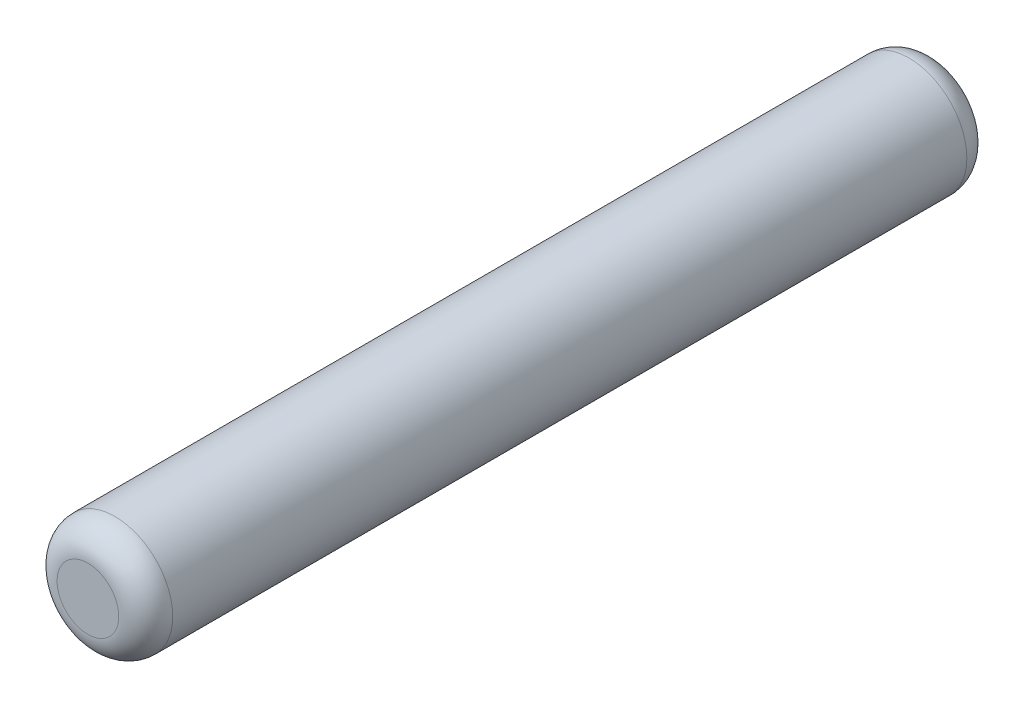
SolidWorks part; units mm, degrees
ref_plane "Front" through (0, 0, 0) normal (0, 0, 1) x (1, 0, 0)
ref_plane "Top" through (0, 0, 0) normal (0, 1, 0) x (1, 0, 0)
ref_plane "Right" through (0, 0, 0) normal (1, 0, 0) x (0, 0, -1)
sketch "Sketch1" plane through (0, 0, 0) normal (0, 0, 1) x (1, 0, 0)
  circle A0 centre (0, 0) radius 0.75
  dimension "D1" = 1.5
extrude "Boss-Extrude1" add sketch "Sketch1" along normal mid plane 11
fillet "Fillet1" radius 0.35 2 edges at (0.75, 0, -5.5) (0.75, 0, 5.5)
